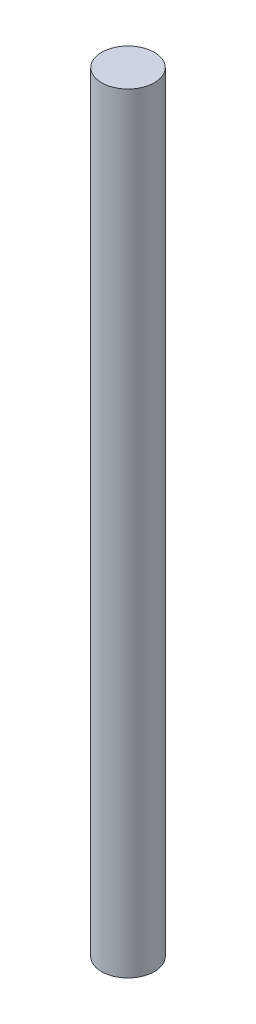
SolidWorks part; units mm, degrees
ref_plane "Front Plane" through (0, 0, 0) normal (0, 0, 1) x (1, 0, 0)
ref_plane "Top Plane" through (0, 0, 0) normal (0, 1, 0) x (1, 0, 0)
ref_plane "Right Plane" through (0, 0, 0) normal (1, 0, 0) x (0, 0, -1)
sketch "Sketch1" plane through (0, 0, 0) normal (0, 1, 0) x (1, 0, 0)
  circle A0 centre (0, 0) radius 2.5
  dimension "D1" = 5
extrude "Extrude1" add sketch "Sketch1" along normal blind 73
